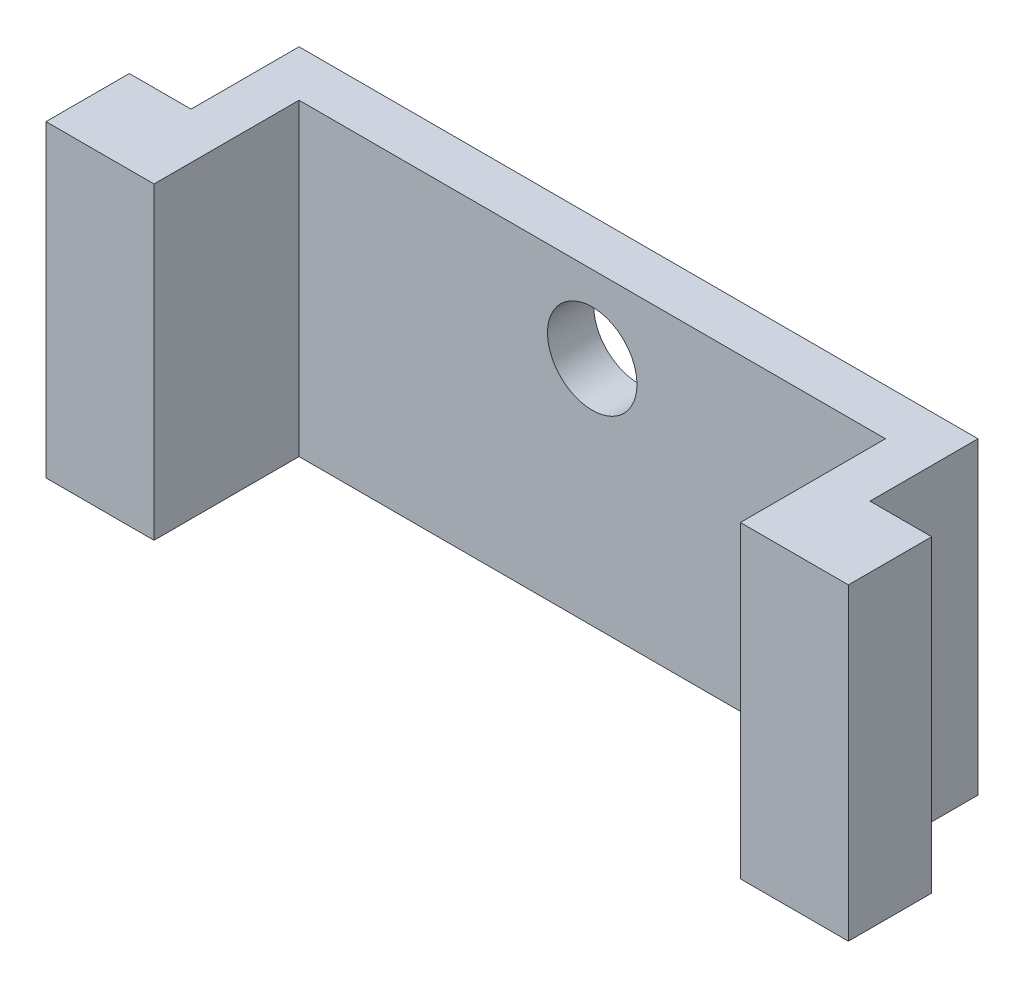
SolidWorks part; units mm, degrees
ref_plane "Front Plane" through (0, 0, 0) normal (0, 0, 1) x (1, 0, 0)
ref_plane "Top Plane" through (0, 0, 0) normal (0, 1, 0) x (1, 0, 0)
ref_plane "Right Plane" through (0, 0, 0) normal (1, 0, 0) x (0, 0, -1)
sketch "Sketch1" plane through (0, 0, 0) normal (0, 1, 0) x (1, 0, 0)
  line L1 (-4.5436, -5.1568) -> (17.4564, -5.1568)
  line L2 (-4.5436, -5.1568) -> (-4.5436, -3.6568)
  line L3 (-4.5436, -3.6568) -> (17.4564, -3.6568)
  line L4 (17.4564, -5.1568) -> (17.4564, -3.6568)
  line L5 (-4.5436, -3.6568) -> (-3.0436, -3.6568)
  line L6 (-4.5436, -3.6568) -> (-4.5436, -9.1568)
  line L7 (-4.5436, -9.1568) -> (-3.0436, -9.1568)
  line L8 (-3.0436, -3.6568) -> (-3.0436, -9.1568)
  line L9 (17.4564, -3.6568) -> (15.9564, -3.6568)
  line L10 (17.4564, -3.6568) -> (17.4564, -9.1568)
  line L11 (17.4564, -9.1568) -> (15.9564, -9.1568)
  line L12 (15.9564, -3.6568) -> (15.9564, -9.1568)
  point P4 (17.4564, -4.4068)
  dimension "D1" = 22
  dimension "D2" = 1.5
  dimension "D3" = 4
  dimension "D4" = 4
  dimension "D5" = 1.5
  dimension "D6" = 1.5
extrude "Boss-Extrude1" add sketch "Sketch1" along normal blind 5 contours L12 L3 L8 L1 | L8 L3 L2 L1 | L8 L1 L6 L7 | L3 L12 L1 L4 | L1 L12 L11 L10
sketch "Sketch2" plane through (0, 5, 0) normal (0, 1, 0) x (1, 0, 0)
  line L1 (-3.0436, -9.1568) -> (-6.5436, -9.1568)
  line L2 (-3.0436, -9.1568) -> (-3.0436, -7.1568)
  line L3 (-3.0436, -7.1568) -> (-6.5436, -7.1568)
  line L4 (-6.5436, -9.1568) -> (-6.5436, -7.1568)
  line L5 (15.9564, -9.1568) -> (19.4564, -9.1568)
  line L6 (15.9564, -9.1568) -> (15.9564, -7.1568)
  line L7 (15.9564, -7.1568) -> (19.4564, -7.1568)
  line L8 (19.4564, -9.1568) -> (19.4564, -7.1568)
  dimension "D1" = 3.5
  dimension "D2" = 3.5
  dimension "D3" = 2
  dimension "D4" = 2
extrude "Boss-Extrude2" add sketch "Sketch2" against normal blind 5
sketch "Sketch3" plane through (0, 0, 5.1568) normal (0, 0, 1) x (1, 0, 0)
  line L1 (15.9564, 5) -> (15.9564, 0) construction
  line L2 (-3.0436, 0) -> (15.9564, 0) construction
  circle A0 centre (6.4564, 2.5) radius 1.45
  dimension "D1" = 9.5
  dimension "D2" = 2.5
  dimension "D3" = 2.9
extrude "Cut-Extrude1" cut sketch "Sketch3" against normal blind 5
sketch "Sketch4" plane through (0, 0, 0) normal (0, -1, 0) x (1, 0, 0)
  line L12 (17.4564, 3.6568) -> (17.4564, 7.1568)
  line L13 (17.4564, 7.1568) -> (19.4564, 7.1568)
  line L14 (19.4564, 7.1568) -> (19.4564, 9.1568)
  line L15 (19.4564, 9.1568) -> (15.9564, 9.1568)
  line L16 (15.9564, 9.1568) -> (15.9564, 5.1568)
  line L17 (15.9564, 5.1568) -> (-3.0436, 5.1568)
  line L18 (-3.0436, 5.1568) -> (-3.0436, 9.1568)
  line L19 (-3.0436, 9.1568) -> (-6.5436, 9.1568)
  line L20 (-6.5436, 9.1568) -> (-6.5436, 7.1568)
  line L21 (-6.5436, 7.1568) -> (-4.5436, 7.1568)
  line L22 (-4.5436, 7.1568) -> (-4.5436, 3.6568)
  line L23 (-4.5436, 3.6568) -> (17.4564, 3.6568)
  line L24 (17.4564, 3.6568) -> (17.4564, 7.1568)
  line L25 (17.4564, 7.1568) -> (19.4564, 7.1568)
  line L26 (19.4564, 7.1568) -> (19.4564, 9.1568)
  line L27 (19.4564, 9.1568) -> (15.9564, 9.1568)
  line L28 (15.9564, 9.1568) -> (15.9564, 5.1568)
  line L29 (15.9564, 5.1568) -> (-3.0436, 5.1568)
  line L30 (-3.0436, 5.1568) -> (-3.0436, 9.1568)
  line L31 (-3.0436, 9.1568) -> (-6.5436, 9.1568)
  line L32 (-6.5436, 9.1568) -> (-6.5436, 7.1568)
  line L33 (-6.5436, 7.1568) -> (-4.5436, 7.1568)
  line L34 (-4.5436, 7.1568) -> (-4.5436, 3.6568)
  line L35 (-4.5436, 3.6568) -> (17.4564, 3.6568)
  dimension "D1" = 0
extrude "Boss-Extrude3" add sketch "Sketch4" along normal blind 5
sketch "Sketch5" plane through (0, 0, 9.1568) normal (0, 0, 1) x (1, 0, 0)
  line L0 (15.9564, 5) -> (15.9564, -5) construction
  line L1 (15.9564, -5) -> (19.4564, -5) construction
  line L2 (19.4564, -5) -> (19.4564, 5) construction
  line L3 (19.4564, 5) -> (15.9564, 5) construction
  line L4 (-6.5436, 5) -> (-6.5436, -5) construction
  line L5 (-6.5436, -5) -> (-3.0436, -5) construction
  line L6 (-3.0436, -5) -> (-3.0436, 5) construction
  line L7 (-3.0436, 5) -> (-6.5436, 5) construction
  line L8 (15.9564, 5) -> (15.9564, -5)
  line L9 (15.9564, -5) -> (19.4564, -5)
  line L10 (19.4564, -5) -> (19.4564, 5)
  line L11 (19.4564, 5) -> (15.9564, 5)
  line L12 (-6.5436, 5) -> (-6.5436, -5)
  line L13 (-6.5436, -5) -> (-3.0436, -5)
  line L14 (-3.0436, -5) -> (-3.0436, 5)
  line L15 (-3.0436, 5) -> (-6.5436, 5)
extrude "Boss-Extrude4" add sketch "Sketch5" along normal blind 0.7
